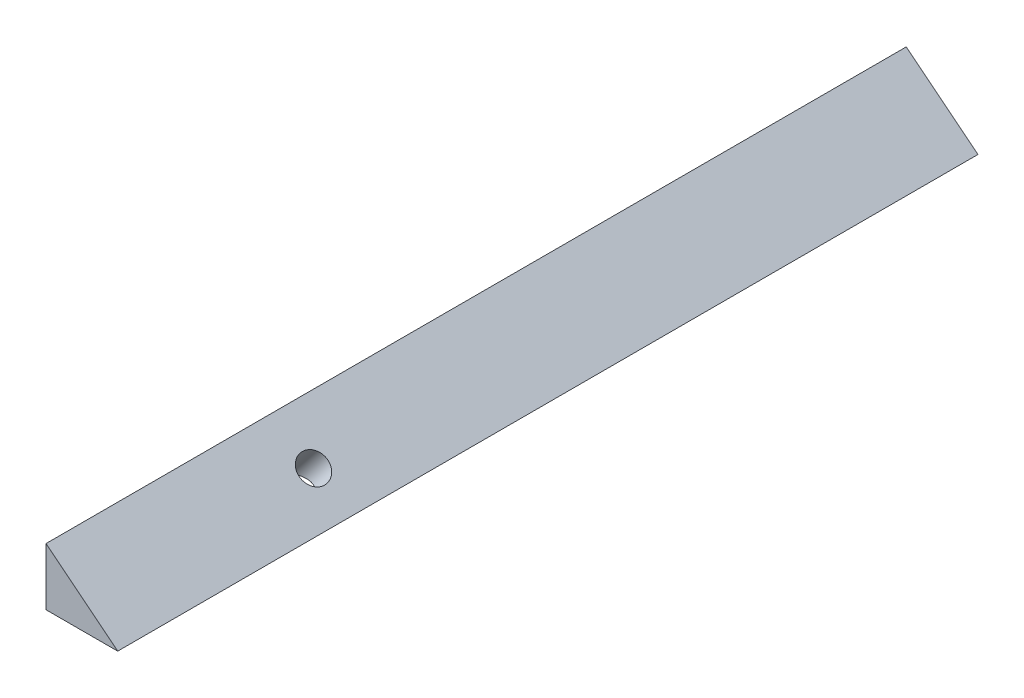
SolidWorks part; units mm, degrees
material "Cast Carbon Steel"
ref_plane "Front Plane" through (0, 0, 0) normal (0, 0, 1) x (1, 0, 0)
ref_plane "Top Plane" through (0, 0, 0) normal (0, 1, 0) x (1, 0, 0)
ref_plane "Right Plane" through (0, 0, 0) normal (1, 0, 0) x (0, 0, -1)
sketch "Sketch1" plane through (0, 0, 0) normal (0, 0, 1) x (1, 0, 0)
  line L0 (63.5, 0) -> (0, 50.8)
  line L1 (0, 0) -> (63.5, 0)
  line L2 (0, 0) -> (0, 50.8)
  line L3 (0, 50.8) -> (63.5, 50.8)
  line L4 (63.5, 0) -> (63.5, 50.8)
  dimension "D1" = 50.8
  dimension "D2" = 63.5
extrude "Boss-Extrude1" add sketch "Sketch1" against normal blind 38.1 contours L2 L1 L0
sketch "Sketch3" plane through (0, 0, 0) normal (0, 0, 1) x (1, 0, 0)
  line L0 (0, 50.8) -> (0, 0)
  line L1 (0, 0) -> (63.5, 0)
  line L2 (63.5, 0) -> (0, 50.8)
extrude "Boss-Extrude2" add sketch "Sketch3" along normal blind 292.1
sketch "Sketch4" plane through (0, 0, -38.1) normal (0, 0, -1) x (-1, 0, 0)
  line L0 (0, 50.8) -> (-63.5, 0)
  line L1 (-63.5, 0) -> (0, 0)
  line L2 (0, 0) -> (0, 50.8)
extrude "Boss-Extrude3" add sketch "Sketch4" along normal blind 431.8
sketch "Sketch6" plane through (24.7805, 30.9756, 0) normal (0.6247, 0.7809, 0) x (0.7809, -0.6247, 0)
  line L0 (49.5852, 469.9) -> (49.5852, -292.1) construction
  line L1 (49.5852, -292.1) -> (-31.7345, -292.1) construction
  circle A0 centre (11.4852, -88.9) radius 12.7
  dimension "D1" = 25.4
  dimension "D3" = 203.2
  dimension "D2" = 38.1
extrude "Cut-Extrude2" cut sketch "Sketch6" against normal blind 431.8
